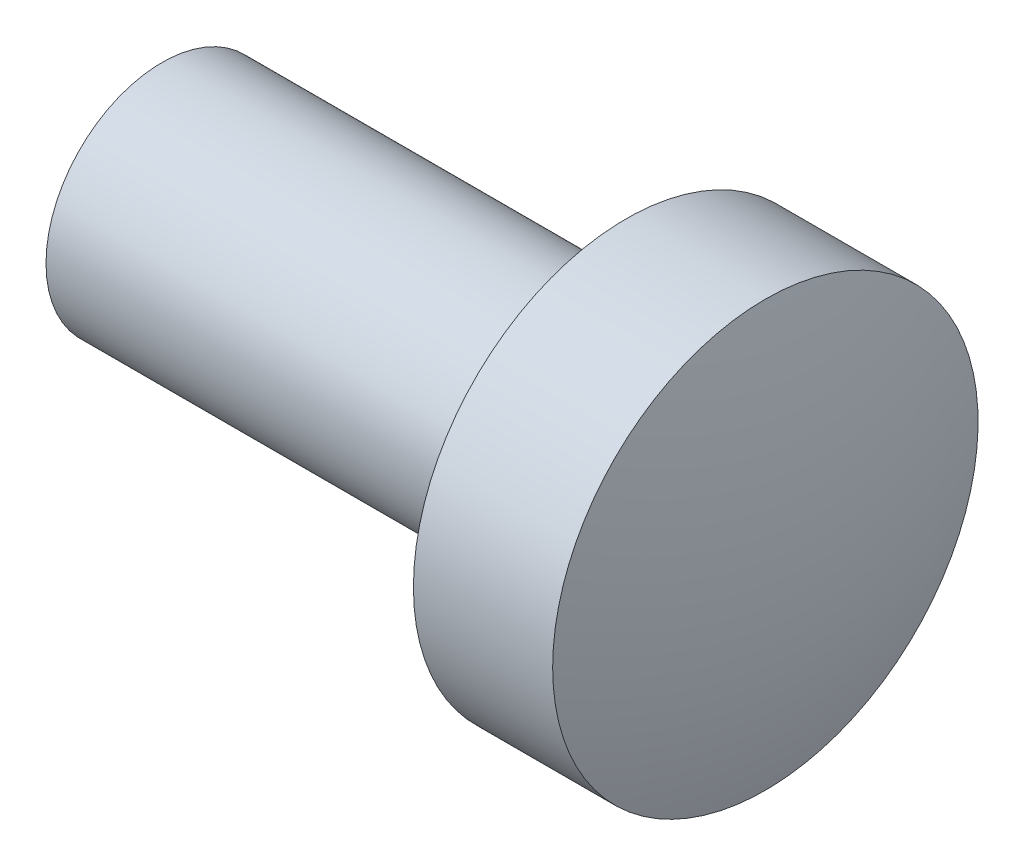
SolidWorks part; units mm, degrees
ref_plane "Plan de face" through (0, 0, 0) normal (0, 0, 1) x (1, 0, 0)
ref_plane "Plan de dessus" through (0, 0, 0) normal (0, 1, 0) x (1, 0, 0)
ref_plane "Plan de droite" through (0, 0, 0) normal (1, 0, 0) x (0, 0, -1)
sketch "Esquisse1" plane through (0, 0, 0) normal (0, 0, 1) x (1, 0, 0)
  line L0 (-16.3014, 0) -> (11.4267, 0) construction
  line L1 (0, 1.5) -> (0, 2.75)
  line L2 (0, 2.75) -> (1.8, 2.75)
  line L3 (2.2, 0) -> (-6, 0)
  line L4 (-6, 0) -> (-6, 1.5)
  line L5 (-6, 1.5) -> (0, 1.5)
  arc A0 (1.8, 2.75) -> (2.2, 0) centre (-7.4531, 0) cw
  dimension "D1" = 6
  dimension "D2" = 3
  dimension "D3" = 5.5
  dimension "D4" = 2.2
  dimension "D5" = 1.8
revolve "Révolution1" add sketch "Esquisse1" angle 360 about L0
